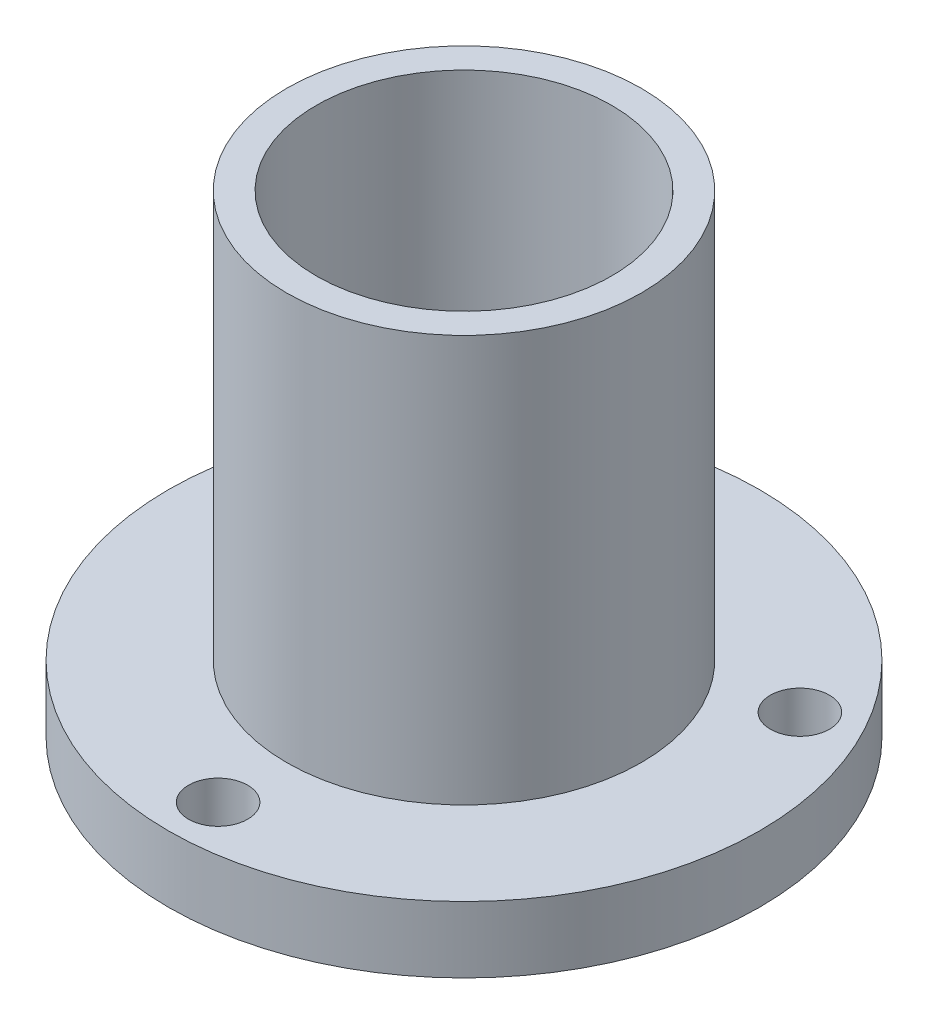
SolidWorks part; units mm, degrees
ref_plane "Front Plane" through (0, 0, 0) normal (0, 0, 1) x (1, 0, 0)
ref_plane "Top Plane" through (0, 0, 0) normal (0, 1, 0) x (1, 0, 0)
ref_plane "Right Plane" through (0, 0, 0) normal (1, 0, 0) x (0, 0, -1)
sketch "Sketch1" plane through (0, 0, 0) normal (0, 1, 0) x (1, 0, 0)
  circle A0 centre (0, 0) radius 7.9375
extrude "Boss-Extrude1" add sketch "Sketch1" along normal blind 1.778
sketch "Sketch2" plane through (0, 1.778, 0) normal (0, 1, 0) x (1, 0, 0)
  circle A0 centre (0, 0) radius 4.7625
extrude "Boss-Extrude2" add sketch "Sketch2" along normal blind 10.922
sketch "Sketch4" plane through (0, 0, 0) normal (0, -1, 0) x (1, 0, 0)
  circle A0 centre (0, 0) radius 3.9688
extrude "Cut-Extrude3" cut sketch "Sketch4" against normal through all and the other way through all
sketch "Sketch7" plane through (0, 0, 0) normal (0, -1, 0) x (1, 0, 0)
  circle A0 centre (0, 6.604) radius 0.7938
  circle A1 centre (5.7192, -3.302) radius 0.7938
  circle A2 centre (-5.7192, -3.302) radius 0.7938
  point P10 (0, 0)
  dimension "D1" = 1.5875
  dimension "D2" = 6.604
  dimension "D3" = 0
  dimension "D4" = 3
extrude "Cut-Extrude5" cut sketch "Sketch7" against normal through all
